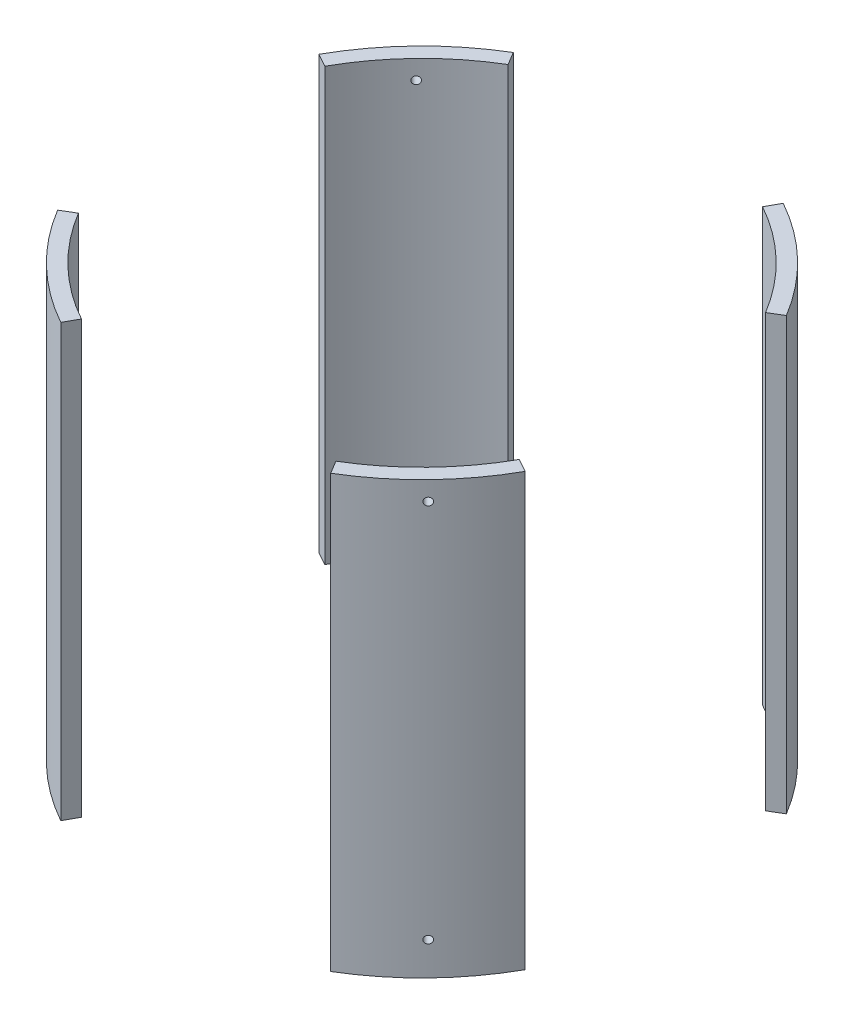
SolidWorks part; units mm, degrees
material "6061-T6 (SS)"
ref_plane "Front Plane" through (0, 0, 0) normal (0, 0, 1) x (1, 0, 0)
ref_plane "Top Plane" through (0, 0, 0) normal (0, 1, 0) x (1, 0, 0)
ref_plane "Right Plane" through (0, 0, 0) normal (1, 0, 0) x (0, 0, -1)
sketch "Sketch2" plane through (0, 0, 0) normal (0, 1, 0) x (1, 0, 0)
  circle A0 centre (0, 0) radius 88.9
  circle A1 centre (0, 0) radius 83.82
  dimension "D1" = 177.8
  dimension "D2" = 167.64
extrude "Boss-Extrude1" add sketch "Sketch2" along normal mid plane 144.4447
sketch "Sketch3" plane through (0, 0, 0) normal (0, 1, 0) x (1, 0, 0)
  line L0 (0, 0) -> (169.6618, 101.6776)
  line L1 (-58.1167, 96.9749) -> (0, 0)
  line L2 (0, 0) -> (53.9, 96.9749)
  line L3 (53.9, 96.9749) -> (-58.1167, 96.9749)
  line L4 (0, 0) -> (70.9917, -118.4586)
  line L5 (70.9917, -118.4586) -> (-65.8409, -118.4586)
  line L6 (-65.8409, -118.4586) -> (0, 0)
  line L7 (169.6618, 101.6776) -> (169.6618, -94.3004)
  line L8 (169.6618, -94.3004) -> (0, 0)
  line L9 (0, 0) -> (-123.7413, 68.7771)
  line L10 (-123.7413, 68.7771) -> (-123.7413, -74.1577)
  line L11 (-123.7413, -74.1577) -> (0, 0)
  dimension "D1" = 60
  dimension "D2" = 60
  dimension "D3" = 60
  dimension "D4" = 60
  dimension "D5" = 30
  dimension "D6" = 30
extrude "Cut-Extrude1" cut sketch "Sketch3" against normal through all both and the other way through all contours L8 L7 L0 | L2 L3 L1 | L10 L11 L9 | L6 L5 L4
ref_plane "Bolt reference plane" through (-56.3092, 0, 58.1758) normal (0.6955, 0, -0.7185) x (-0.7185, 0, -0.6955)
sketch "Sketch5" plane through (-56.3092, 0, 58.1758) normal (0.6955, 0, -0.7185) x (-0.7185, 0, -0.6955)
  line L0 (-23.009, -72.2224) -> (23.009, -72.2224) construction
  circle A0 centre (-0.0228, 65.8724) radius 1.27
  circle A1 centre (-0.0228, -61.1099) radius 1.27
  dimension "D1" = 2.54
  dimension "D4" = 11.1125
  dimension "D2" = 21.717
  dimension "D3" = 6.35
extrude "Bolt holes" cut sketch "Sketch5" against normal through all
pattern_circular "Bolt pattern" count 4 over 360 about axis through (0, 72.2224, 0) along (0, 1, 0) of "Bolt holes"
equation "\"D1@Boss-Extrude1\"=3*12"
